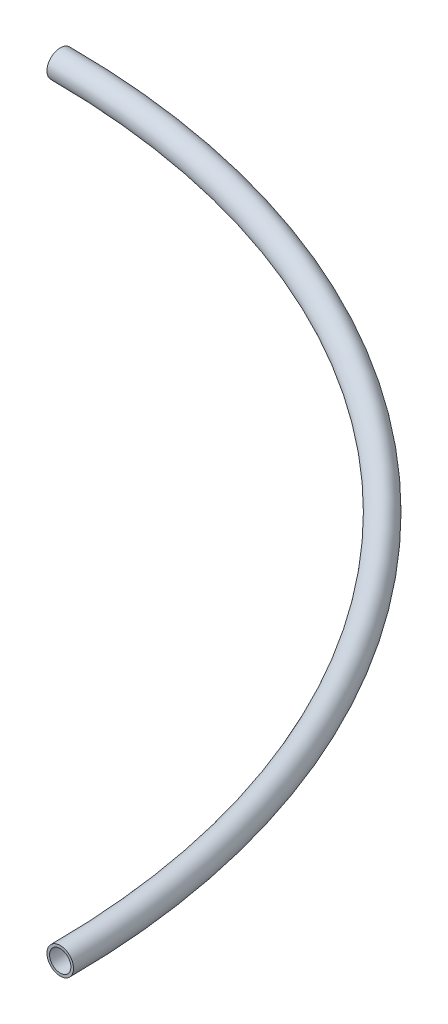
SolidWorks part; units mm, degrees
material "AISI 1020"
ref_plane "Front Plane" through (0, 0, 0) normal (0, 0, 1) x (1, 0, 0)
ref_plane "Top Plane" through (0, 0, 0) normal (0, 1, 0) x (1, 0, 0)
ref_plane "Right Plane" through (0, 0, 0) normal (1, 0, 0) x (0, 0, -1)
sketch "Sketch1" plane through (0, 0, 0) normal (0, 0, 1) x (1, 0, 0)
  line L0 (0, 0) -> (1460, 0)
  line L1 (0, 0) -> (0, 929.7724) construction
  circle A0 centre (1460, 0) radius 25
  circle A1 centre (1460, 0) radius 20
revolve "Revolve1" add sketch "Sketch1" angle 90 about L1
